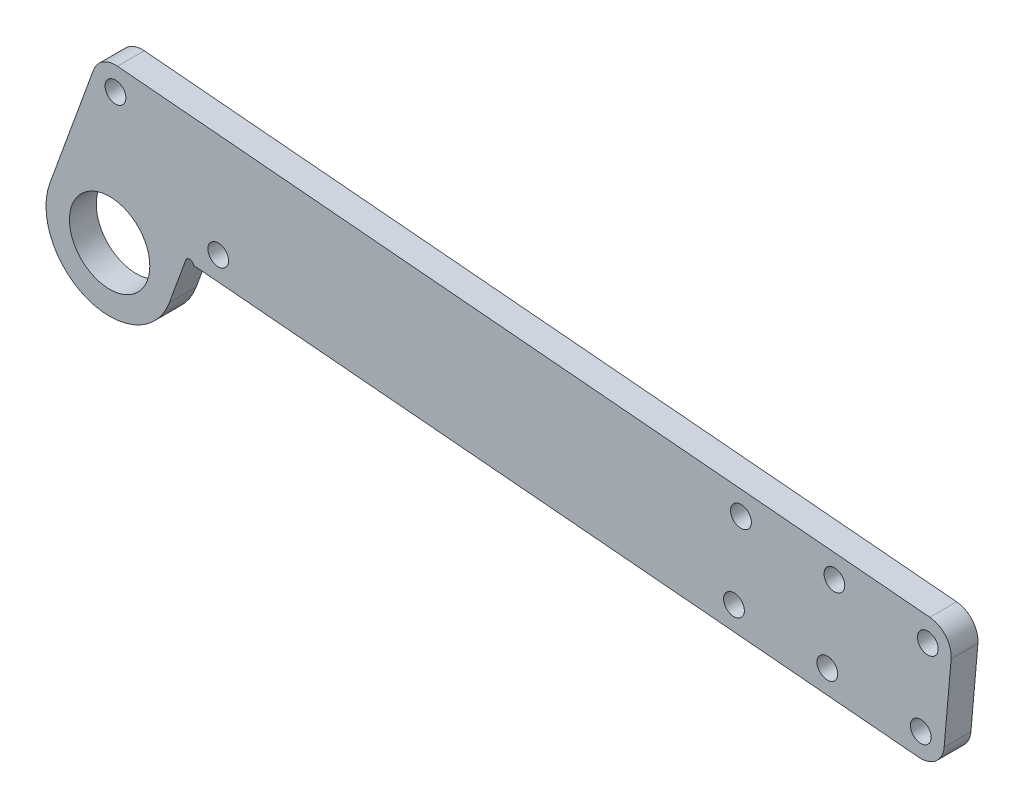
SolidWorks part; units mm, degrees
ref_plane "前视基准面" through (0, 0, 0) normal (0, 0, 1) x (1, 0, 0)
ref_plane "上视基准面" through (0, 0, 0) normal (0, 1, 0) x (1, 0, 0)
ref_plane "右视基准面" through (0, 0, 0) normal (1, 0, 0) x (0, 0, -1)
sketch "草图1" plane through (0, 0, 0) normal (0, 0, 1) x (1, 0, 0)
  line L0 (0, 0) -> (160, 0) construction
  line L1 (-8.9271, 3.2492) -> (-1.4962, 23.6654)
  line L2 (-1.4962, 23.6654) -> (160.828, 9.4638)
  line L3 (8.9271, -3.2492) -> (11.3716, 3.467)
  line L4 (11.3716, 3.467) -> (159.172, -9.4638)
  circle A0 centre (0, 0) radius 6
  arc A1 (-8.9271, 3.2492) -> (8.9271, -3.2492) centre (0, 0) ccw
  arc A2 (159.172, -9.4638) -> (160.828, 9.4638) centre (160, 0) ccw
  circle A3 centre (160, 0) radius 6
  dimension "D1" = 12
  dimension "D2" = 19
  dimension "D3" = 160
  dimension "D4" = 70
  dimension "D5" = 5
extrude "凸台-拉伸1" add sketch "草图1" along normal mid plane 4
sketch "草图2" plane through (0, 0, 2) normal (0, 0, 1) x (1, 0, 0)
  line L0 (8.9271, -3.2492) -> (11.3716, 3.467) construction
  line L1 (160.828, 9.4638) -> (-1.4962, 23.6654) construction
  line L2 (-1.4962, 23.6654) -> (-8.9271, 3.2492) construction
  line L3 (11.3716, 3.467) -> (159.172, -9.4638) construction
  circle A0 centre (0.8742, 19.9446) radius 1.55
  circle A1 centre (16.2206, 6.5562) radius 1.55
  circle A2 centre (11.9354, 3.2618) radius 0.6
  dimension "D1" = 3.5
  dimension "D2" = 3.5
  dimension "D3" = 3.5
  dimension "D4" = 3.5
  dimension "D5" = 3.1
  dimension "D6" = 1.2
extrude "切除-拉伸1" cut sketch "草图2" against normal through all
fillet "圆角1" radius 3.5 1 edges at (-1.4962, 23.6654, 0)
sketch "草图3" plane through (0, 0, 2) normal (0, 0, 1) x (1, 0, 0)
  line L0 (125.9612, 12.5143) -> (124.3052, -6.4134)
  line L1 (160.828, 9.4638) -> (1.1792, 23.4313) construction
  line L2 (12.5263, 3.366) -> (159.172, -9.4638) construction
  line L3 (124.3052, -6.4134) -> (159.172, -9.4638)
  line L4 (160.828, 9.4638) -> (125.9612, 12.5143)
  arc A0 (159.172, -9.4638) -> (160.828, 9.4638) centre (160, 0) ccw
  dimension "D1" = 35
extrude "切除-拉伸2" cut sketch "草图3" against normal through all
sketch "草图4" plane through (0, 0, 2) normal (0, 0, 1) x (1, 0, 0)
  line L0 (122.1694, 9.3327) -> (121.1236, -2.6217) construction
  line L1 (94.276, 11.773) -> (93.2301, -0.1813) construction
  line L2 (125.9612, 12.5143) -> (124.3052, -6.4134) construction
  line L3 (91.0944, 15.5648) -> (89.4384, -3.3629) construction
  line L4 (125.9612, 12.5143) -> (1.1792, 23.4313) construction
  line L5 (12.5263, 3.366) -> (124.3052, -6.4134) construction
  line L6 (90.2664, 6.1009) -> (93.7531, 5.7959) construction
  line L7 (93.7531, 5.7959) -> (121.6465, 3.3555) construction
  line L8 (108.2227, 10.5528) -> (107.1768, -1.4015) construction
  circle A0 centre (122.1694, 9.3327) radius 1.55
  circle A1 centre (121.1236, -2.6217) radius 1.55
  circle A2 centre (94.276, 11.773) radius 1.55
  circle A3 centre (93.2301, -0.1813) radius 1.55
  circle A4 centre (108.2227, 10.5528) radius 1.55
  circle A5 centre (107.1768, -1.4015) radius 1.55
  point P23 (107.6998, 4.5757)
  point P24 (108.2364, 10.7098)
  dimension "D1" = 35
  dimension "D3" = 3.5
  dimension "D5" = 3.5
  dimension "D6" = 3.1
  dimension "D2" = 3.5
  dimension "D4" = 3.5
extrude "切除-拉伸3" cut sketch "草图4" against normal through all
fillet "圆角2" radius 3.5 2 edges at (124.3052, -6.4134, 0) (125.9612, 12.5143, 0)
